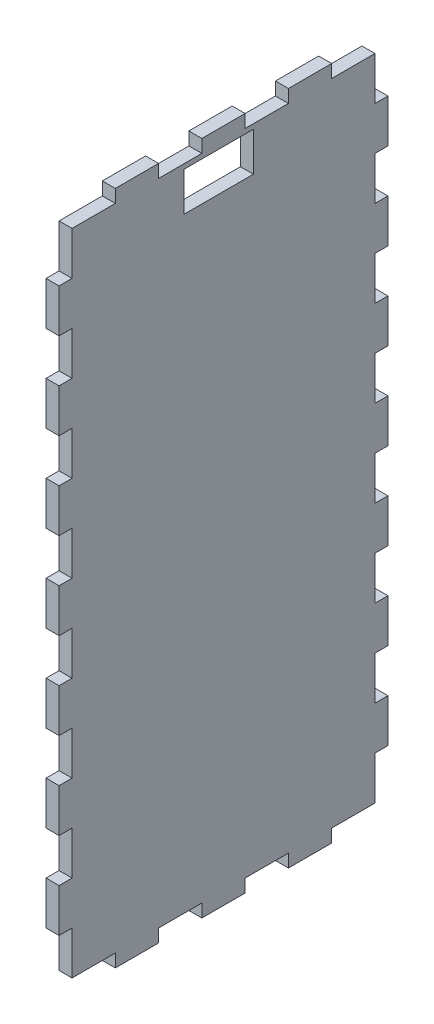
SolidWorks part; units mm, degrees
ref_plane "Front Plane" through (0, 0, 0) normal (0, 0, 1) x (1, 0, 0)
ref_plane "Top Plane" through (0, 0, 0) normal (0, 1, 0) x (1, 0, 0)
ref_plane "Right Plane" through (0, 0, 0) normal (1, 0, 0) x (0, 0, -1)
sketch "Sketch1" plane through (0, 0, 0) normal (1, 0, 0) x (0, 0, -1)
  line L0 (41.909, 148.8936) -> (25.909, 148.8936)
  line L1 (10, 153.0059) -> (20, 153.0059)
  line L2 (0, 140) -> (0, 150.0059)
  line L3 (0, 150.0059) -> (10, 150.0059)
  line L4 (10, 150.0059) -> (10, 153.0059)
  line L5 (-3, 120) -> (0, 120)
  line L6 (-3, 130) -> (-3, 140)
  line L7 (0, 130) -> (-3, 130)
  line L8 (0, 120) -> (0, 130)
  line L9 (-3, 100) -> (0, 100)
  line L10 (-3, 110) -> (-3, 120)
  line L11 (0, 110) -> (-3, 110)
  line L12 (-3, 140) -> (0, 140)
  line L13 (0, 100) -> (0, 110)
  line L14 (-3, 80) -> (0, 80)
  line L15 (-3, 90) -> (-3, 100)
  line L16 (0, 90) -> (-3, 90)
  line L17 (0, 80) -> (0, 90)
  line L18 (-3, 60) -> (0, 60)
  line L19 (-3, 70) -> (-3, 80)
  line L20 (0, 70) -> (-3, 70)
  line L21 (0, 60) -> (0, 70)
  line L22 (-3, 40) -> (0, 40)
  line L23 (-3, 50) -> (-3, 60)
  line L24 (0, 50) -> (-3, 50)
  line L25 (0, 40) -> (0, 50)
  line L26 (-3, 20) -> (0, 20)
  line L27 (-3, 30) -> (-3, 40)
  line L28 (0, 30) -> (-3, 30)
  line L29 (0, 20) -> (0, 30)
  line L30 (-3, 10) -> (-3, 20)
  line L31 (20, 153.0059) -> (20, 150.0059)
  line L32 (0, 10) -> (-3, 10)
  line L33 (0, 0) -> (0, 10)
  line L34 (20, 150.0059) -> (30, 150.0059)
  line L35 (30, 153.0059) -> (40, 153.0059)
  line L36 (30, 150.0059) -> (30, 153.0059)
  line L37 (40, 153.0059) -> (40, 150.0059)
  line L38 (40, 150.0059) -> (50, 150.0059)
  line L39 (50, 153.0059) -> (60, 153.0059)
  line L40 (50, 150.0059) -> (50, 153.0059)
  line L41 (60, 153.0059) -> (60, 150.0059)
  line L42 (60, 150.0059) -> (70, 150.0059)
  line L43 (41.909, 148.8936) -> (41.909, 139.8936)
  line L44 (41.909, 139.8936) -> (25.909, 139.8936)
  line L45 (25.909, 139.8936) -> (25.909, 148.8936)
  line L49 (70, 0) -> (70, 10)
  line L50 (70, 10) -> (73, 10)
  line L51 (73, 10) -> (73, 20)
  line L52 (70, 20) -> (70, 30)
  line L53 (70, 30) -> (73, 30)
  line L54 (73, 30) -> (73, 40)
  line L55 (73, 20) -> (70, 20)
  line L56 (70, 40) -> (70, 50)
  line L57 (70, 50) -> (73, 50)
  line L58 (73, 50) -> (73, 60)
  line L59 (73, 40) -> (70, 40)
  line L60 (70, 60) -> (70, 70)
  line L61 (70, 70) -> (73, 70)
  line L62 (73, 70) -> (73, 80)
  line L63 (73, 60) -> (70, 60)
  line L64 (70, 80) -> (70, 90)
  line L65 (70, 90) -> (73, 90)
  line L66 (73, 90) -> (73, 100)
  line L67 (73, 80) -> (70, 80)
  line L68 (70, 100) -> (70, 110)
  line L69 (73, 140) -> (70, 140)
  line L70 (70, 110) -> (73, 110)
  line L71 (73, 110) -> (73, 120)
  line L72 (73, 100) -> (70, 100)
  line L73 (70, 120) -> (70, 130)
  line L74 (70, 130) -> (73, 130)
  line L75 (73, 130) -> (73, 140)
  line L76 (73, 120) -> (70, 120)
  line L77 (70, 140) -> (70, 150.0059)
  line L80 (60, 0) -> (70, 0)
  line L81 (60, -3) -> (60, 0)
  line L82 (50, 0) -> (50, -3)
  line L83 (50, -3) -> (60, -3)
  line L84 (40, 0) -> (50, 0)
  line L85 (40, -3) -> (40, 0)
  line L86 (30, 0) -> (30, -3)
  line L87 (30, -3) -> (40, -3)
  line L88 (20, 0) -> (30, 0)
  line L89 (20, -3) -> (20, 0)
  line L90 (10, 0) -> (10, -3)
  line L91 (0, 0) -> (10, 0)
  line L92 (10, -3) -> (20, -3)
extrude "Boss-Extrude1" add sketch "Sketch1" along normal blind 3
